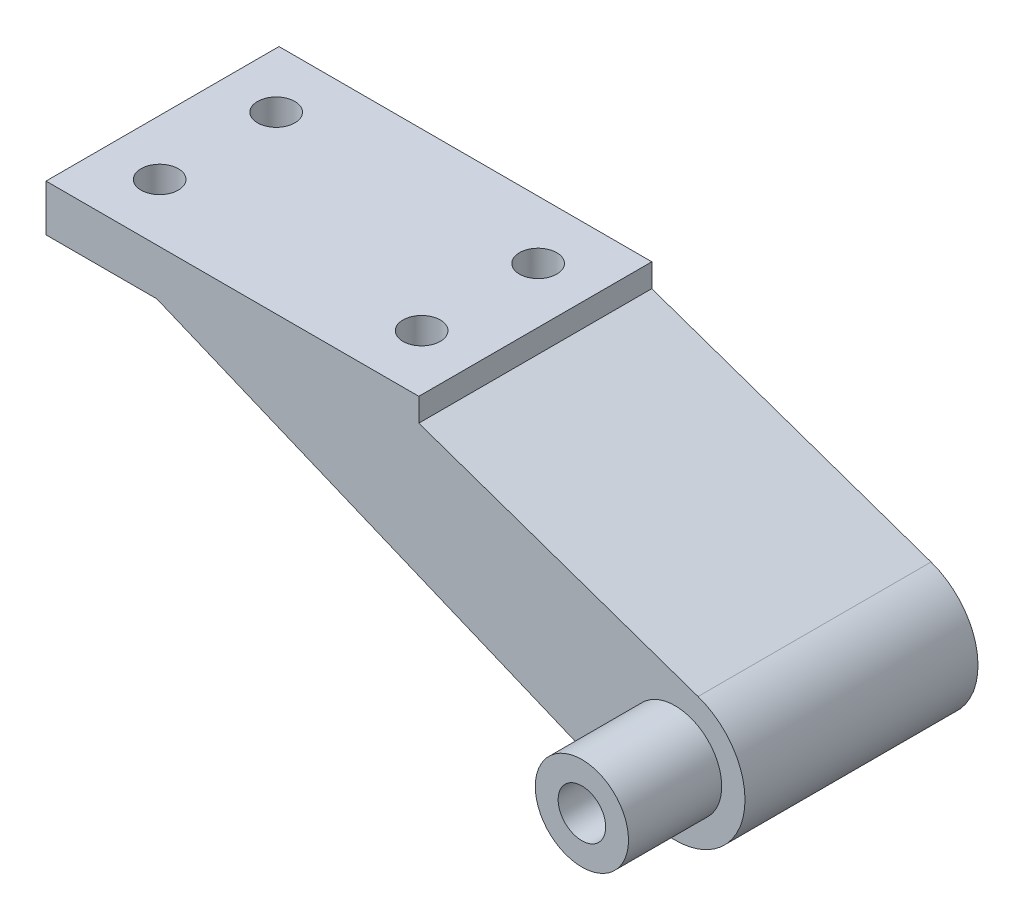
SolidWorks part; units mm, degrees
ref_plane "Front Plane" through (0, 0, 0) normal (0, 0, 1) x (1, 0, 0)
ref_plane "Top Plane" through (0, 0, 0) normal (0, 1, 0) x (1, 0, 0)
ref_plane "Right Plane" through (0, 0, 0) normal (1, 0, 0) x (0, 0, -1)
sketch "Sketch1" plane through (0, 0, 0) normal (0, 1, 0) x (1, 0, 0)
  line L1 (0, 0) -> (50.8, 0)
  line L2 (0, 0) -> (0, 31.75)
  line L3 (0, 31.75) -> (50.8, 31.75)
  line L4 (50.8, 0) -> (50.8, 31.75)
  dimension "D1" = 50.8
  dimension "D2" = 31.75
extrude "Boss-Extrude1" add sketch "Sketch1" along normal blind 6.35
sketch "Sketch2" plane through (0, 0, 0) normal (0, 0, 1) x (1, 0, 0)
  line L0 (0, 0) -> (50.8, 0) construction
  circle A0 centre (85.725, -19.05) radius 3.175 construction
  circle A1 centre (85.725, -19.05) radius 3.175 construction
  circle A2 centre (85.725, -19.05) radius 3.2385
  circle A3 centre (85.725, -19.05) radius 9.525
  dimension "D1" = 6.477
  dimension "D2" = 19.05
  dimension "D3" = 85.725
  dimension "D4" = 19.05
extrude "Boss-Extrude2" add sketch "Sketch2" against normal up to surface (31.75 mm away) separate body up to face at (25.4, 3.175, -31.75)
sketch "Sketch3" plane through (0, 0, 0) normal (0, 0, 1) x (1, 0, 0)
  line L0 (50.8, 3.175) -> (88.8526, -10.0531)
  line L1 (50.8, 6.35) -> (50.8, 0) construction
  line L2 (82.0678, -27.8449) -> (15.105, 0)
  line L3 (0, 0) -> (50.8, 0) construction
  line L4 (15.105, 0) -> (15.105, 3.175)
  line L5 (15.105, 3.175) -> (50.8, 3.175)
  circle A1 centre (85.725, -19.05) radius 9.525 construction
  arc A2 (88.8526, -10.0531) -> (82.0678, -27.8449) centre (85.725, -19.05) ccw
extrude "Boss-Extrude3" add sketch "Sketch3" against normal up to surface (31.75 mm away) up to face at (25.4, 3.175, -31.75)
sketch "Sketch4" plane through (0, 0, 0) normal (0, 0, 1) x (1, 0, 0)
  circle A0 centre (85.725, -19.05) radius 3.2385
  circle A1 centre (85.725, -19.05) radius 6.35
extrude "Boss-Extrude4" add sketch "Sketch4" along normal blind 12.7
sketch "Sketch5" plane through (0, 0, 0) normal (0, -1, 0) x (1, 0, 0)
  line L0 (7.5525, 0) -> (7.5525, -7.9375) construction
  line L1 (0, 0) -> (15.105, 0) construction
  line L2 (7.5525, -7.9375) -> (7.5525, -15.875) construction
  line L3 (7.5525, -15.875) -> (7.5525, -23.8125) construction
  line L4 (7.5525, -23.8125) -> (7.5525, -31.75) construction
  line L5 (15.105, -31.75) -> (0, -31.75) construction
  circle A0 centre (7.5525, -7.9375) radius 2.54
  circle A1 centre (7.5525, -23.8125) radius 2.54
  dimension "D1" = 5.08
extrude "Cut-Extrude1" cut sketch "Sketch5" against normal up to next
sketch "Sketch6" plane through (0, 6.35, 0) normal (0, 1, 0) x (1, 0, 0)
  line L0 (7.5525, 7.9375) -> (0, 7.9375) construction
  line L1 (0, 31.75) -> (0, 0) construction
  line L2 (50.8, 7.9375) -> (43.2475, 7.9375) construction
  line L3 (50.8, 0) -> (50.8, 31.75) construction
  line L4 (7.5525, 23.8125) -> (43.2475, 23.8125) construction
  line L5 (43.2475, 23.8125) -> (43.2475, 7.9375) construction
  circle A0 centre (43.2475, 7.9375) radius 2.54
  circle A1 centre (43.2475, 23.8125) radius 2.54
  circle A2 centre (7.5525, 7.9375) radius 2.54 construction
extrude "Cut-Extrude2" cut sketch "Sketch6" against normal through all
ref_plane "Plane9" through (0, -19.05, 0) normal (0, 1, 0) x (1, 0, 0)
sketch "Sketch7" plane through (0, -19.05, 0) normal (0, 1, 0) x (1, 0, 0)
  circle A0 centre (43.2475, 7.9375) radius 2.54 construction
  circle A1 centre (43.2475, 23.8125) radius 2.54 construction
  circle A2 centre (43.2475, 7.9375) radius 2.54 construction
  circle A3 centre (43.2475, 23.8125) radius 2.54 construction
  circle A4 centre (43.2475, 23.8125) radius 4.7625
  circle A5 centre (43.2475, 7.9375) radius 4.7625
  dimension "D1" = 9.525
extrude "Cut-Extrude3" cut sketch "Sketch7" along normal up to surface (19.05 mm away) up to face at (7.5525, 0, -26.3525)
